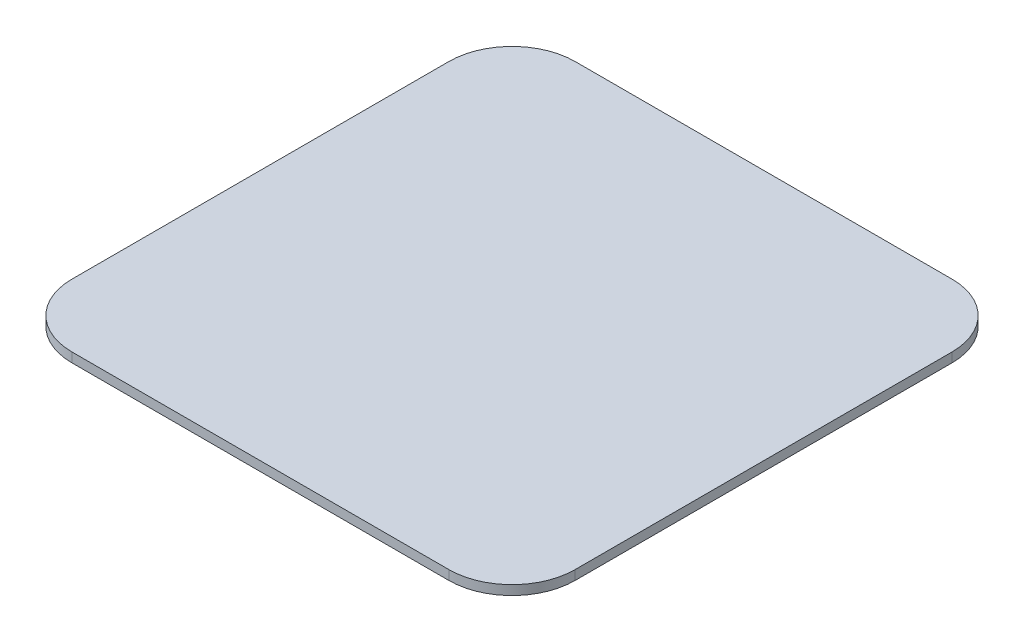
SolidWorks part; units mm, degrees
material "PMMA"
ref_plane "前视基准面" through (0, 0, 0) normal (0, 0, 1) x (1, 0, 0)
ref_plane "上视基准面" through (0, 0, 0) normal (0, 1, 0) x (1, 0, 0)
ref_plane "右视基准面" through (0, 0, 0) normal (1, 0, 0) x (0, 0, -1)
sketch "草图1" plane through (0, 0, 0) normal (0, 1, 0) x (1, 0, 0)
  line L1 (79.75, -79.75) -> (-79.75, -79.75)
  line L2 (79.75, -79.75) -> (79.75, 79.75)
  line L3 (79.75, 79.75) -> (-79.75, 79.75)
  line L4 (-79.75, -79.75) -> (-79.75, 79.75)
  line L5 (79.75, -79.75) -> (-79.75, 79.75) construction
  line L6 (79.75, 79.75) -> (-79.75, -79.75) construction
  point P0 (0, 0)
  dimension "D1" = 159.5
  dimension "D2" = 159.5
extrude "凸台-拉伸1" add sketch "草图1" along normal blind 3
fillet "圆角1" radius 20 4 edges at (-79.75, 1.5, -79.75) (79.75, 1.5, -79.75) (79.75, 1.5, 79.75) (-79.75, 1.5, 79.75)
sketch "草图2" plane through (0, 0, 0) normal (0, 0, 1) x (1, 0, 0)
  line L0 (0, 3) -> (0, 0)
  line L1 (-59.75, 3) -> (59.75, 3) construction
